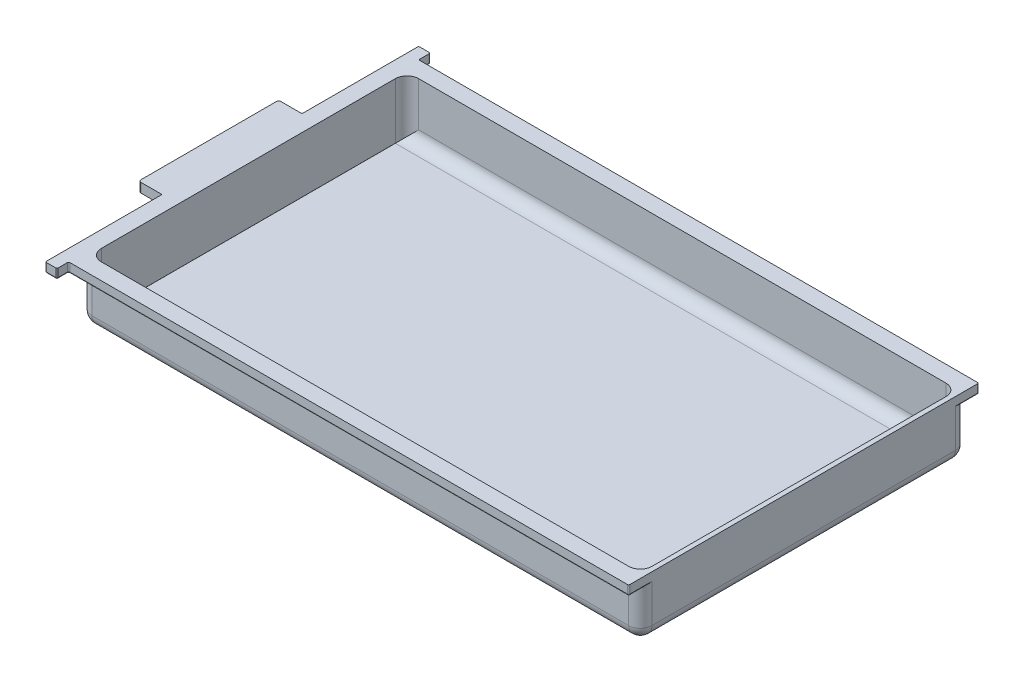
SolidWorks part; units mm, degrees
material "ABS"
ref_plane "Front Plane" through (0, 0, 0) normal (0, 0, 1) x (1, 0, 0)
ref_plane "Top Plane" through (0, 0, 0) normal (0, 1, 0) x (1, 0, 0)
ref_plane "Right Plane" through (0, 0, 0) normal (1, 0, 0) x (0, 0, -1)
sketch "Sketch2" plane through (0, 0, 0) normal (0, 1, 0) x (1, 0, 0)
  line L1 (-120, -70) -> (120, -70)
  line L2 (-120, -70) -> (-120, 70)
  line L3 (-120, 70) -> (120, 70)
  line L4 (120, -70) -> (120, 70)
  line L5 (-120, -70) -> (120, 70) construction
  line L6 (-120, 70) -> (120, -70) construction
  point P0 (0, 0)
  dimension "D1" = 140
  dimension "D2" = 240
extrude "Boss-Extrude1" add sketch "Sketch2" along normal blind 1
sketch "Sketch3" plane through (0, 1, 0) normal (0, 1, 0) x (1, 0, 0)
  line L0 (-120, 70) -> (-120, -70) construction
  line L1 (-120, -70) -> (120, -70) construction
  line L2 (120, -70) -> (120, 70) construction
  line L3 (120, 70) -> (-120, 70) construction
  line L4 (-120, 70) -> (-120, -70)
  line L5 (-120, -70) -> (120, -70)
  line L6 (120, -70) -> (120, 70)
  line L7 (120, 70) -> (-120, 70)
  line L9 (118, -68) -> (-118, -68)
  line L10 (118, -68) -> (118, 68)
  line L11 (118, 68) -> (-118, 68)
  line L12 (-118, -68) -> (-118, 68)
  line L13 (118, -68) -> (-118, 68) construction
  line L14 (118, 68) -> (-118, -68) construction
  point P2 (0, 0)
  dimension "D1" = 2
  dimension "D2" = 2
extrude "Boss-Extrude2" add sketch "Sketch3" along normal blind 20
sketch "Sketch4" plane through (0, 21, 0) normal (0, 1, 0) x (1, 0, 0)
  line L0 (118, 68) -> (-118, 68) construction
  line L1 (118, 68) -> (-118, 68)
  line L4 (-125, 80) -> (-120, 80)
  line L5 (-120, 80) -> (-120, 75)
  line L6 (-120, 75) -> (120, 75)
  line L10 (-1000, 0) -> (49000, 0) construction
  line L11 (-125, 80) -> (-125, 30)
  line L12 (-125, 30) -> (-135, 30)
  line L13 (-135, 30) -> (-135, -30)
  line L14 (120, 75) -> (120, -75)
  line L15 (120, -70) -> (120, 70) construction
  line L16 (-125, -30) -> (-135, -30)
  line L17 (-125, -80) -> (-125, -30)
  line L18 (-125, -80) -> (-120, -80)
  line L19 (-120, -80) -> (-120, -75)
  line L20 (-120, -75) -> (120, -75)
  line L21 (118, -68) -> (118, 68) construction
  line L22 (-118, -68) -> (118, -68) construction
  line L23 (-118, 68) -> (-118, -68) construction
  line L24 (118, -68) -> (118, 68)
  line L25 (-118, -68) -> (118, -68)
  line L26 (-118, 68) -> (-118, -68)
  point P8 (-122.5, 80)
  point P17 (-135, 0)
  point P22 (120, 0)
  dimension "D1" = 7
  dimension "D2" = 5
  dimension "D3" = 30
  dimension "D4" = 80
  dimension "D5" = 10
  dimension "D6" = 240
  dimension "D7" = 236
extrude "Boss-Extrude3" add sketch "Sketch4" along normal blind 4
sketch "Sketch6" plane through (0, 21, 0) normal (0, -1, 0) x (1, 0, 0)
  line L0 (-135, -30) -> (-135, 30) construction
  line L1 (-133, 28) -> (-122, 28)
  line L2 (-133, 28) -> (-133, -28)
  line L3 (-133, -28) -> (-122, -28)
  line L4 (-122, 28) -> (-122, -28)
  line L5 (-133, 28) -> (-122, -28) construction
  line L6 (-133, -28) -> (-122, 28) construction
  line L7 (-120, -70) -> (-120, 70) construction
  line L8 (-125, -30) -> (-135, -30) construction
  line L9 (-135, 30) -> (-125, 30) construction
  point P0 (-127.5, 0)
  dimension "D1" = 2
  dimension "D2" = 2
  dimension "D3" = 2
  dimension "D4" = 2
extrude "Cut-Extrude2" cut sketch "Sketch6" against normal blind 3
fillet "Fillet1" radius 5 8 edges at (0, 1, -68) (118, 1, 0) (0, 1, 68) (-120, 0, 0) (118, 13, 68) (-118, 13, 68) (-118, 13, -68) (118, 13, -68)
fillet "Fillet2" radius 5 9 edges at (2.5, 0, 70) (-118.5355, 1.4645, 70) (2.5, 0, -70) (-118.5355, 1.4645, -70) (-120, 13, 70) (-120, 13, -70) (120, 10.5, -70) (120, 10.5, 70) (120, 0, 0)
fillet "Fillet3" radius 0.5 18 edges at (-120, 23, -75) (-120, 23, -80) (-125, 23, -80) (120, 23, -75) (120, 23, 75) (-120, 23, 75) (-122.5, 21, -80) (-120, 21, -77.5) (-125, 21, -55) (120, 21, -70) (120, 21, 70) (0, 21, -75) (0, 21, 75) (-125, 21, 55) (-125, 23, 80) (-122.5, 21, 80) (-120, 23, 80) (-120, 21, 77.5)
fillet "Fillet4" radius 1 10 edges at (-133, 22.5, 28) (-133, 22.5, -28) (-122, 22.5, -28) (-122, 22.5, 28) (-127.5, 24, -28) (-133, 24, 0) (-127.5, 24, 28) (-122, 24, 0) (-135, 23, 30) (-135, 23, -30)
